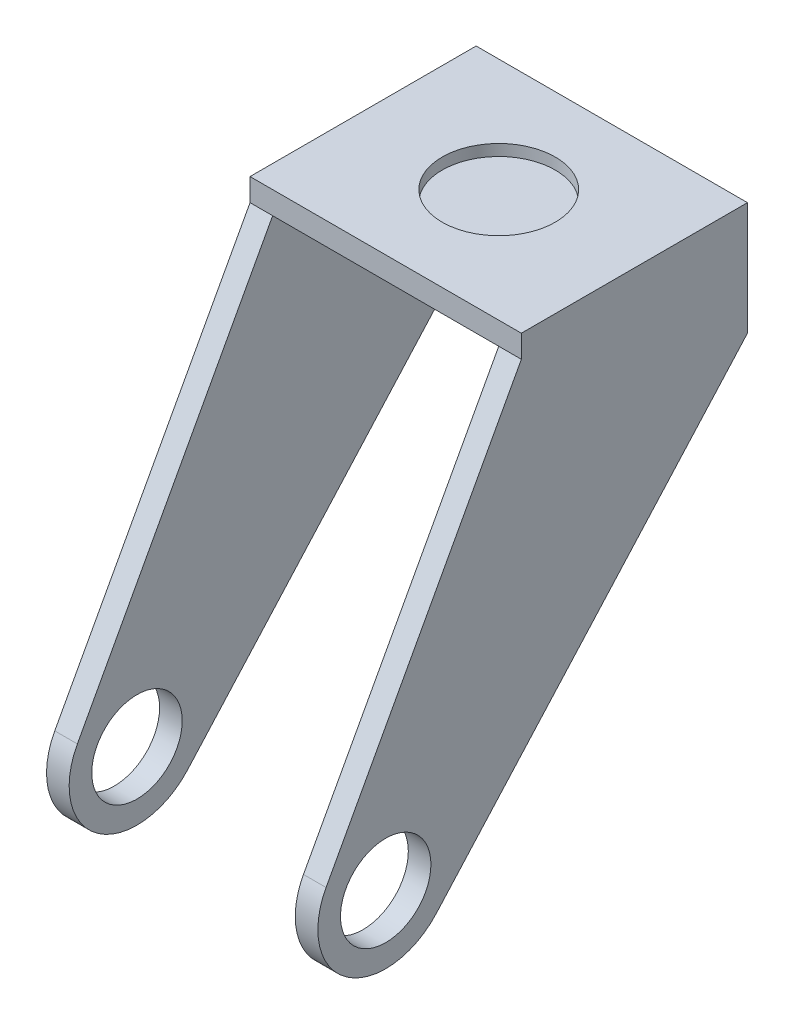
SolidWorks part; units mm, degrees
ref_plane "Front Plane" through (0, 0, 0) normal (0, 0, 1) x (1, 0, 0)
ref_plane "Top Plane" through (0, 0, 0) normal (0, 1, 0) x (1, 0, 0)
ref_plane "Right Plane" through (0, 0, 0) normal (1, 0, 0) x (0, 0, -1)
sketch "Sketch1" plane through (0, 0, 0) normal (1, 0, 0) x (0, 0, -1)
  line L0 (0, 0) -> (50, 0)
  line L1 (50, 0) -> (50, -20)
  line L2 (0, 0) -> (-43.1833, -79.5669)
  line L3 (-18.8268, -96.7356) -> (50, -20)
  arc A1 (-43.1833, -79.5669) -> (-18.8268, -96.7356) centre (-29.9981, -86.7228) ccw
  circle A2 centre (-29.9981, -86.7228) radius 10
  dimension "D3" = 90.53
  dimension "D7" = 20
  dimension "D1" = 50
  dimension "D2" = 20
  dimension "D4" = 138.11
  dimension "D5" = 118.49
  dimension "D6" = 103.08
extrude "Boss-Extrude3" add sketch "Sketch1" along normal blind 5
ref_plane "Plane3" through (30, 0, 0) normal (1, 0, 0) x (0, 0, -1)
mirror "Mirror6" about plane through (30, 0, 0) normal (1, 0, 0) of bodies 105
sketch "Sketch3" plane through (0, 0, 0) normal (0, 1, 0) x (1, 0, 0)
  line L0 (0, 0) -> (0, 50)
  line L1 (0, 50) -> (60, 50)
  line L2 (60, 50) -> (60, 0)
  line L3 (60, 0) -> (0, 0)
extrude "Boss-Extrude4" add sketch "Sketch3" along normal blind 5
sketch "Sketch9" plane through (0, 5, 0) normal (0, 1, 0) x (1, 0, 0)
  line L0 (0, 25) -> (60, 25) construction
  line L1 (0, 50) -> (0, 0) construction
  line L2 (60, 0) -> (60, 50) construction
  circle A0 centre (30, 25) radius 12.5
  dimension "D1" = 25
extrude "Cut-Extrude3" cut sketch "Sketch9" against normal blind 2.5
